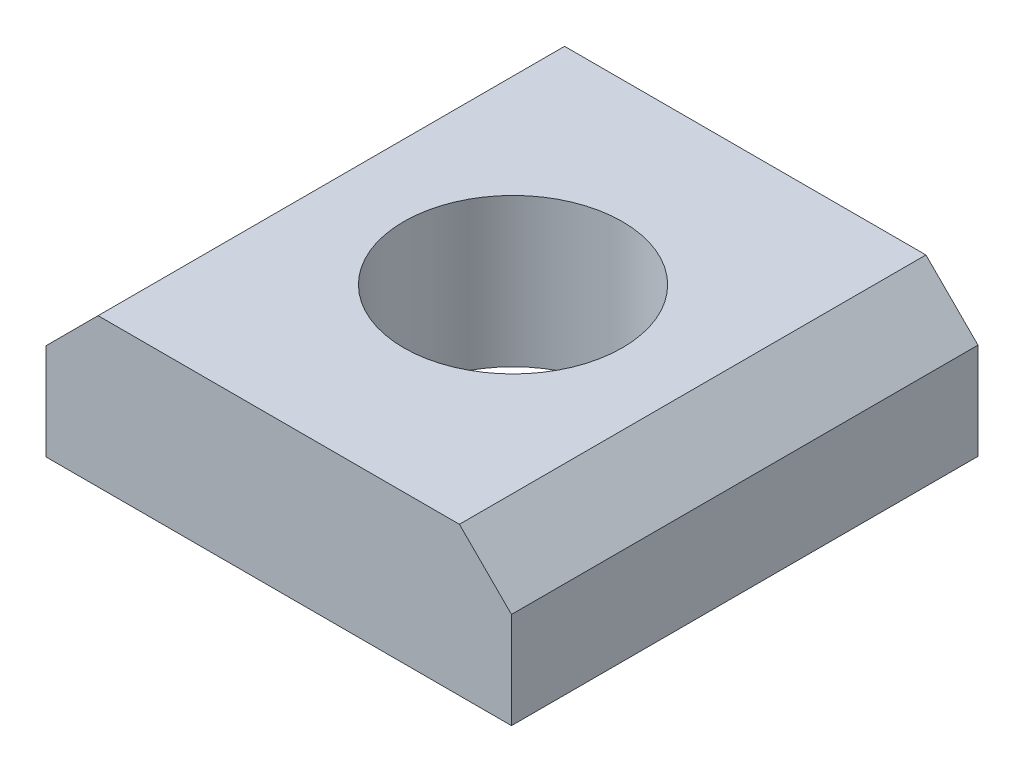
SolidWorks part; units mm, degrees
material "AISI 1020"
ref_plane "Front Plane" through (0, 0, 0) normal (0, 0, 1) x (1, 0, 0)
ref_plane "Top Plane" through (0, 0, 0) normal (0, 1, 0) x (1, 0, 0)
ref_plane "Right Plane" through (0, 0, 0) normal (1, 0, 0) x (0, 0, -1)
sketch "Sketch1" plane through (0, 0, 0) normal (0, 1, 0) x (1, 0, 0)
  line L1 (-4.47, 4.46) -> (4.47, 4.46)
  line L2 (-4.47, 4.46) -> (-4.47, -4.5)
  line L3 (-4.47, -4.5) -> (4.47, -4.5)
  line L4 (4.47, 4.46) -> (4.47, -4.5)
  dimension "D3" = 4.47
  dimension "D1" = 8.96
  dimension "D2" = 8.94
extrude "Extrude1" add sketch "Sketch1" along normal blind 2.85
sketch "Sketch2" plane through (0, 2.85, 0) normal (0, 1, 0) x (1, 0, 0)
  point P0 (0, 0)
  point P1 (-6.9777, 3.3701)
hole_wizard "M5x0.8 Tapped Hole1" positions "Sketch4" profile "Sketch3" tap size "M5x0.8" standard "ANSI Metric"
sketch "Sketch4" plane through (0, 2.85, 0) normal (0, 1, 0) x (1, 0, 0)
  point P0 (0, 0)
sketch "Sketch3" plane through (0, 2.85, 0) normal (1, 0, 0) x (0, 0, 1)
  line L0 (0, 0) -> (0, 13.6618)
  line L1 (0, 13.6618) -> (2.1, 12.4)
  line L2 (2.1, 12.4) -> (2.1, 0)
  line L5 (2.1, 0) -> (0, 0)
  line L10 (0, 13.6618) -> (-2.1, 12.4) construction
  line L11 (0, -6.35) -> (0, 107.95) construction
  dimension "Tap Drill Dia." = 4.2
  dimension "Tap Drill Depth" = 12.4
  dimension "Drill Angle" = 118
cosmetic thread "Hole Thread1" parameters "D1"=2.85, "D2"=5
chamfer "Chamfer1" distance 1 angle 45 2 edges at (4.47, 2.85, 0.02) (-4.47, 2.85, 0.02)
